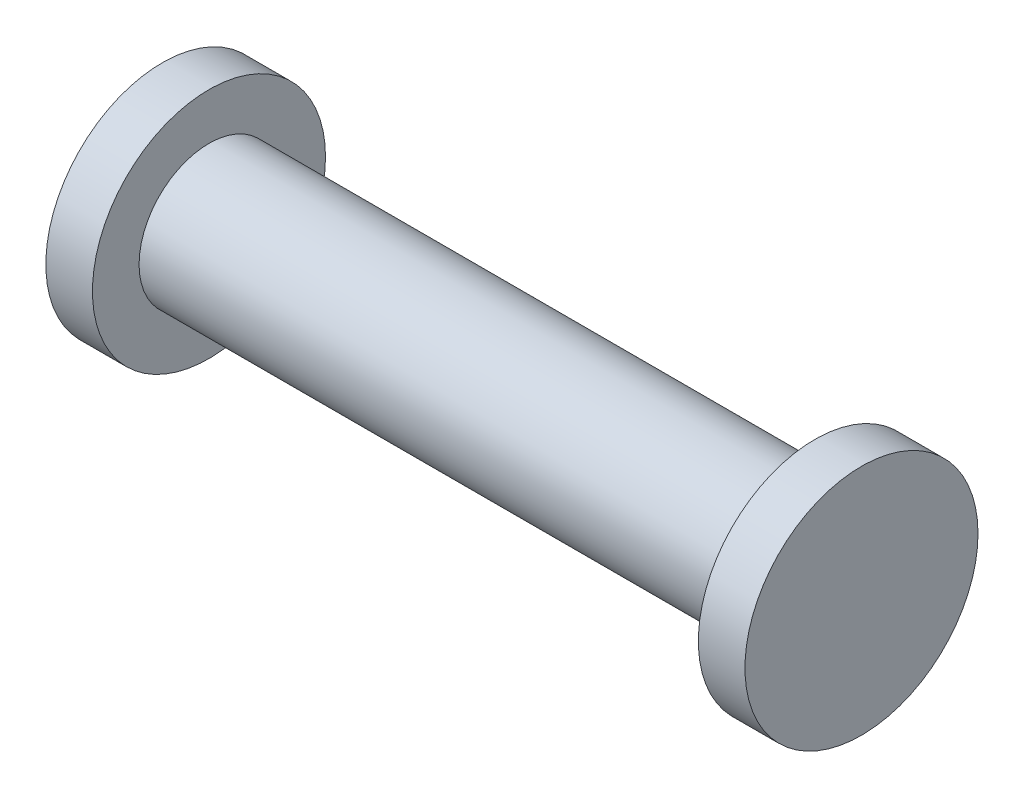
SolidWorks part; units mm, degrees
ref_plane "Front Plane" through (0, 0, 0) normal (0, 0, 1) x (1, 0, 0)
ref_plane "Top Plane" through (0, 0, 0) normal (0, 1, 0) x (1, 0, 0)
ref_plane "Right Plane" through (0, 0, 0) normal (1, 0, 0) x (0, 0, -1)
sketch "Sketch1" plane through (0, 0, 0) normal (1, 0, 0) x (0, 0, -1)
  circle A0 centre (0, 0) radius 7.5
  dimension "D2" = 0
extrude "Boss-Extrude1" add sketch "Sketch1" along normal mid plane 0 separate body
sketch "Sketch4" plane through (32.5, 0, 0) normal (1, 0, 0) x (0, 0, -1)
  circle A0 centre (0, 0) radius 12.5
  dimension "D1" = 0
extrude "Boss-Extrude3" add sketch "Sketch4" along normal blind 5 separate body
mirror "Mirror1" about plane through (0, 0, 0) normal (1, 0, 0) of "Boss-Extrude3"
